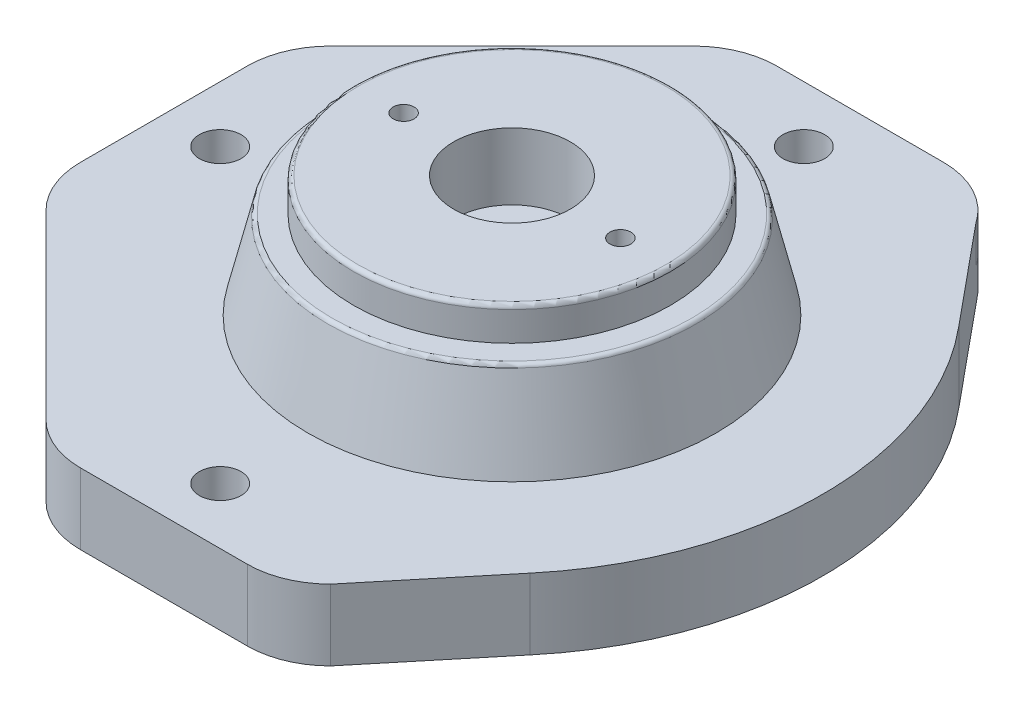
SolidWorks part; units mm, degrees
ref_plane "Front Plane" through (0, 0, 0) normal (0, 0, 1) x (1, 0, 0)
ref_plane "Top Plane" through (0, 0, 0) normal (0, 1, 0) x (1, 0, 0)
ref_plane "Right Plane" through (0, 0, 0) normal (1, 0, 0) x (0, 0, -1)
sketch "Sketch1" plane through (0, 0, 0) normal (1, 0, 0) x (0, 0, -1)
  line L0 (0, 32.7122) -> (0, -12.7527) construction
  line L2 (0, 2) -> (51, 2)
  line L3 (0, 0) -> (51, 0)
  line L4 (51, 2) -> (51, 0)
  line L6 (0, 18) -> (44, 18)
  line L7 (44, 18) -> (51, 2)
  line L8 (44, 18) -> (44, 32)
  line L9 (44, 32) -> (0, 32)
  dimension "D1" = 14
  dimension "D2" = 44
  dimension "D3" = 51
  dimension "D4" = 16
  dimension "D5" = 2
revolve "Revolve1" add sketch "Sketch1" angle 360 about L0
sketch "Sketch3" plane through (0, 0, 0) normal (1, 0, 0) x (0, 0, -1)
  line L0 (0, -18.7491) -> (0, 62.1181) construction
  line L1 (0, 0) -> (45, 0)
  line L2 (45, 0) -> (45, 2)
  line L3 (-51, 2) -> (51, 2) construction
  line L4 (45, 2) -> (0, 2)
  line L5 (0, 18) -> (41, 18)
  line L6 (-44, 18) -> (44, 18) construction
  line L7 (41, 18) -> (45, 2)
  line L8 (41, 18) -> (41, 32)
  line L9 (44, 32) -> (-44, 32) construction
  line L10 (41, 32) -> (0, 32)
  dimension "D1" = 45
  dimension "D2" = 41
revolve "Cut-Revolve1" cut sketch "Sketch3" angle 360 about L0
sketch "Sketch4" plane through (0, 18, 0) normal (0, -1, 0) x (-1, 0, 0)
  circle A0 centre (0, 0) radius 15
  dimension "D1" = 30
extrude "Boss-Extrude1" add sketch "Sketch4" along normal blind 6
sketch "Sketch5" plane through (0, 12, 0) normal (0, -1, 0) x (1, 0, 0)
  circle A0 centre (0, 0) radius 9.2
  dimension "D1" = 18.4
extrude "Cut-Extrude3" cut sketch "Sketch5" against normal blind 7
sketch "Sketch6" plane through (0, 19, 0) normal (0, -1, 0) x (1, 0, 0)
  circle A0 centre (0, 0) radius 7
  dimension "D1" = 14
extrude "Cut-Extrude4" cut sketch "Sketch6" against normal blind 27
fillet "Fillet1" radius 2 1 edges at (0, 19, -9.2)
sketch "Sketch7" plane through (0, 0, 0) normal (1, 0, 0) x (0, 0, -1)
sketch "Sketch9" plane through (0, 32, 0) normal (0, 1, 0) x (1, 0, 0)
  circle A0 centre (0, 0) radius 38
  circle A1 centre (0, 0) radius 44
  dimension "D1" = 76
extrude "Cut-Extrude6" cut sketch "Sketch9" against normal blind 2
sketch "Sketch13" plane through (0, 32, 0) normal (0, 1, 0) x (1, 0, 0)
  circle A0 centre (0, 0) radius 38
  circle A1 centre (0, 0) radius 7
extrude "Boss-Extrude2" add sketch "Sketch13" along normal blind 6
fillet "Fillet5" radius 1 1 edges at (0, 38, 38)
sketch "Sketch14" plane through (0, 38, 0) normal (0, 1, 0) x (1, 0, 0)
  circle A0 centre (0, 0) radius 7
  circle A1 centre (0, 0) radius 14
  dimension "D1" = 28
extrude "Cut-Extrude9" cut sketch "Sketch14" against normal blind 16
sketch "Sketch15" plane through (0, 0, 0) normal (0, 1, 0) x (1, 0, 0)
  line L0 (0, 0) -> (0, -83.5)
  line L1 (0, 0) -> (0, 83.5)
  line L2 (0, 83.5) -> (20, 83.5)
  line L3 (0, 83.5) -> (-20, 83.5)
  line L4 (20, 83.5) -> (20, 63.5)
  line L5 (-20, 83.5) -> (-20, 63.5)
  line L6 (0, -83.5) -> (20, -83.5)
  line L7 (0, -83.5) -> (-20, -83.5)
  line L8 (20, -83.5) -> (20, -63.5)
  line L9 (-20, -83.5) -> (-20, -63.5)
  line L10 (0, 0) -> (74.5, 0)
  line L11 (0, 0) -> (-74.5, 0)
  line L12 (0, 0) -> (5.5, 0)
  line L13 (0, 0) -> (-5.5, 0)
  line L14 (20, 63.5) -> (34.1421, 77.6421)
  line L15 (-20, 63.5) -> (-34.1421, 77.6421)
  line L16 (-20, -63.5) -> (-34.1421, -77.6421)
  line L17 (20, -63.5) -> (34.1421, -77.6421)
  line L18 (34.1421, 77.6421) -> (55.785, 51.4213)
  line L19 (-34.1421, 77.6421) -> (-55.785, 51.4213)
  line L20 (34.1421, -77.6421) -> (55.785, -51.4213)
  line L21 (-34.1421, -77.6421) -> (-55.785, -51.4213)
  line L22 (0, 0) -> (-70, 0)
  line L23 (-70, 0) -> (-83.5, 0)
  line L24 (-83.5, 0) -> (-83.5, 20)
  line L25 (-83.5, 0) -> (-83.5, -20)
  line L26 (-83.5, 20) -> (-63.5, 20)
  line L27 (-83.5, -20) -> (-63.5, -20)
  line L28 (-63.5, -20) -> (-77.6421, -34.1421)
  line L29 (-63.5, 20) -> (-77.6421, 34.1421)
  line L30 (-77.6421, -34.1421) -> (-34.1421, -77.6421)
  line L31 (-34.1421, 77.6421) -> (-77.6421, 34.1421)
  line L32 (-83.5, -20) -> (-83.5, 20)
  circle A0 centre (20, 63.5) radius 20
  circle A1 centre (-20, 63.5) radius 20
  circle A2 centre (20, -63.5) radius 20
  circle A4 centre (-20, -63.5) radius 20
  circle A6 centre (-5.5, 0) radius 80
  circle A7 centre (5.5, 0) radius 80
  circle A9 centre (-63.5, 20) radius 20
  circle A10 centre (-63.5, -20) radius 20
  dimension "D1" = 70
  dimension "D2" = 13.5
extrude "Boss-Extrude3" add sketch "Sketch15" along normal blind 9
sketch "Sketch16" plane through (0, 0, 0) normal (1, 0, 0) x (0, 0, -1)
  line L0 (0, -11.59) -> (0, 53.3602) construction
  line L1 (0, 0) -> (48, 0)
  line L2 (-51.4213, 0) -> (51.4213, 0) construction
  line L3 (48, 0) -> (48, 2)
  line L4 (48, 2) -> (0, 2)
  line L7 (-44, 18) -> (44, 18) construction
  line L8 (41, 18) -> (48, 2)
  line L9 (15, 18) -> (15, 2)
  line L10 (15, 18) -> (41, 18)
  line L11 (15, 2) -> (15, 12)
  line L12 (15, 12) -> (15, 2)
  line L13 (15, 12) -> (0, 12)
  dimension "D1" = 48
  dimension "D2" = 2
  dimension "D3" = 10
revolve "Cut-Revolve3" cut sketch "Sketch16" angle 360 about L0
sketch "Sketch17" plane through (0, 0, 0) normal (0, -1, 0) x (-1, 0, 0)
  line L0 (0, 0) -> (0, 70)
  line L1 (0, 0) -> (0, -70)
  circle A0 centre (0, 70) radius 5
  circle A1 centre (0, -70) radius 5
  dimension "D3" = 10
  dimension "D4" = 10
  dimension "D1" = 70
  dimension "D2" = 70
extrude "Cut-Extrude11" cut sketch "Sketch17" against normal blind 10
sketch "Sketch21" plane through (0, 0, 0) normal (1, 0, 0) x (0, 0, -1)
  line L0 (0, -11.2722) -> (0, 47.26) construction
  line L1 (0, 9) -> (49, 9)
  line L2 (51.4213, 9) -> (-51.4213, 9) construction
  line L3 (0, 30) -> (44, 30)
  line L4 (44, 30) -> (-44, 30) construction
  line L5 (44, 30) -> (49, 9)
  line L6 (40.9042, 30) -> (45.9042, 9)
  dimension "D1" = 49
  dimension "D2" = 44
revolve "Revolve3" add sketch "Sketch21" angle 360 about L0
fillet "Fillet6" radius 1 1 edges at (0, 30, -44)
sketch "Sketch22" plane through (0, 0, 0) normal (0, -1, 0) x (1, 0, 0)
sketch "Sketch24" plane through (0, 0, 0) normal (0, -1, 0) x (-1, 0, 0)
sketch "Sketch26" plane through (0, 0, 0) normal (1, 0, 0) x (0, 0, -1)
  line L0 (0, -14.8461) -> (0, 48.7332) construction
  line L1 (0, 0) -> (45, 0)
  line L2 (-51.4213, 0) -> (51.4213, 0) construction
  line L3 (45, 0) -> (45, 2)
  line L5 (0, 18) -> (41, 18)
  line L6 (41, 18) -> (45, 2)
  line L7 (45, 2) -> (0, 2)
  line L8 (45, 0) -> (48, 0)
  line L9 (48, 0) -> (48, 2)
  line L10 (48, 2) -> (45, 2)
  line L11 (48, 2) -> (41, 18)
  dimension "D1" = 45
  dimension "D2" = 2
  dimension "D3" = 18
  dimension "D4" = 41
revolve "Revolve4" add sketch "Sketch26" angle 360 about L0
sketch "Sketch29" plane through (0, 0, 0) normal (0, -1, 0) x (-1, 0, 0)
  circle A0 centre (0, 0) radius 45
  circle A1 centre (0, 0) radius 48
  dimension "D1" = 96
extrude "Cut-Extrude12" cut sketch "Sketch29" against normal blind 2
fillet "Fillet7" radius 3 1 edges at (0, 2, -45)
sketch "Sketch34" plane through (0, 0, 0) normal (0, -1, 0) x (1, 0, 0)
  line L0 (0, 0) -> (0, -83.5)
  line L1 (0, 0) -> (0, 83.5)
  line L2 (0, 83.5) -> (20, 83.5)
  line L3 (0, 83.5) -> (-20, 83.5)
  line L4 (20, 83.5) -> (20, 63.5)
  line L5 (-20, 83.5) -> (-20, 63.5)
  line L6 (0, -83.5) -> (20, -83.5)
  line L7 (0, -83.5) -> (-20, -83.5)
  line L8 (20, -83.5) -> (20, -63.5)
  line L9 (-20, -83.5) -> (-20, -63.5)
  line L10 (0, 0) -> (74.5, 0)
  line L11 (0, 0) -> (-74.5, 0)
  line L12 (0, 0) -> (5.5, 0)
  line L13 (0, 0) -> (-5.5, 0)
  line L14 (20, 63.5) -> (34.1421, 77.6421)
  line L15 (-20, 63.5) -> (-34.1421, 77.6421)
  line L16 (-20, -63.5) -> (-34.1421, -77.6421)
  line L17 (20, -63.5) -> (34.1421, -77.6421)
  line L18 (34.1421, 77.6421) -> (55.785, 51.4213)
  line L19 (-34.1421, 77.6421) -> (-55.785, 51.4213)
  line L20 (34.1421, -77.6421) -> (55.785, -51.4213)
  line L21 (-34.1421, -77.6421) -> (-55.785, -51.4213)
  line L22 (0, 0) -> (-83.5, 0)
  line L23 (-83.5, 20) -> (-83.5, -20) construction
  line L24 (-83.5, 0) -> (-83.5, -20)
  line L25 (-83.5, 0) -> (-83.5, 20)
  line L26 (-83.5, -20) -> (-63.5, -20)
  line L27 (-83.5, 20) -> (-63.5, 20)
  line L28 (-83.5, -20) -> (-83.5, 20)
  line L29 (-63.5, -20) -> (-77.6421, -34.1421)
  line L30 (-63.5, 20) -> (-77.6421, 34.1421)
  line L31 (-34.1421, -77.6421) -> (-77.6421, -34.1421)
  line L32 (-77.6421, 34.1421) -> (-34.1421, 77.6421)
  line L33 (-77.6421, -34.1421) -> (-34.1421, -77.6421)
  circle A0 centre (20, 63.5) radius 20
  circle A1 centre (-20, 63.5) radius 20
  circle A2 centre (20, -63.5) radius 20
  circle A3 centre (-20, -63.5) radius 20
  circle A4 centre (-5.5, 0) radius 80
  circle A5 centre (5.5, 0) radius 80
  circle A6 centre (0, 0) radius 48
  circle A7 centre (-63.5, -20) radius 20
  circle A8 centre (-63.5, 20) radius 20
extrude "Boss-Extrude7" add sketch "Sketch34" along normal blind 8
sketch "Sketch35" plane through (0, -8, 0) normal (0, -1, 0) x (-1, 0, 0)
  line L1 (-9.815, 70) -> (-4.9075, 61.5)
  line L2 (-4.9075, 61.5) -> (4.9075, 61.5)
  line L3 (4.9075, 61.5) -> (9.815, 70)
  line L4 (9.815, 70) -> (4.9075, 78.5)
  line L5 (4.9075, 78.5) -> (-4.9075, 78.5)
  line L6 (-4.9075, 78.5) -> (-9.815, 70)
  line L7 (-9.815, -70) -> (-4.9075, -78.5)
  line L8 (-4.9075, -78.5) -> (4.9075, -78.5)
  line L9 (4.9075, -78.5) -> (9.815, -70)
  line L10 (9.815, -70) -> (4.9075, -61.5)
  line L11 (4.9075, -61.5) -> (-4.9075, -61.5)
  line L12 (-4.9075, -61.5) -> (-9.815, -70)
  circle A0 centre (0, 70) radius 8.5 construction
  circle A1 centre (0, -70) radius 8.5 construction
  dimension "D1" = 17
  dimension "D2" = 17
extrude "Cut-Extrude14" cut sketch "Sketch35" against normal blind 8
sketch "Sketch36" plane through (0, 38, 0) normal (0, 1, 0) x (1, 0, 0)
  line L0 (-14, 0) -> (-38, 0)
  line L1 (14, 0) -> (38, 0)
  circle A3 centre (0, 0) radius 14
  circle A4 centre (0, 0) radius 38 construction
  circle A5 centre (-26, 0) radius 2.5
  circle A6 centre (26, 0) radius 2.5
  dimension "D1" = 5
  dimension "D2" = 5
extrude "Cut-Extrude15" cut sketch "Sketch36" against normal blind 18 contours L1 A6 | L1 A6 | L0 A5 | L0 A5
sketch "Sketch38" plane through (0, -8, 0) normal (0, -1, 0) x (-1, 0, 0)
sketch "Sketch39" plane through (0, -8, 0) normal (0, -1, 0) x (-1, 0, 0)
sketch "Sketch40" plane through (0, -8, 0) normal (0, -1, 0) x (1, 0, 0)
  line L0 (0, 0) -> (-70, 0)
  circle A0 centre (-70, 0) radius 5
  dimension "D2" = 10
  dimension "D1" = 70
extrude "Cut-Extrude16" cut sketch "Sketch40" against normal blind 20
sketch "Sketch41" plane through (0, -8, 0) normal (0, -1, 0) x (-1, 0, 0)
  line L1 (70, 9.815) -> (61.5, 4.9075)
  line L2 (61.5, 4.9075) -> (61.5, -4.9075)
  line L3 (61.5, -4.9075) -> (70, -9.815)
  line L4 (70, -9.815) -> (78.5, -4.9075)
  line L5 (78.5, -4.9075) -> (78.5, 4.9075)
  line L6 (78.5, 4.9075) -> (70, 9.815)
  circle A0 centre (70, 0) radius 8.5 construction
extrude "Cut-Extrude17" cut sketch "Sketch41" against normal blind 8
